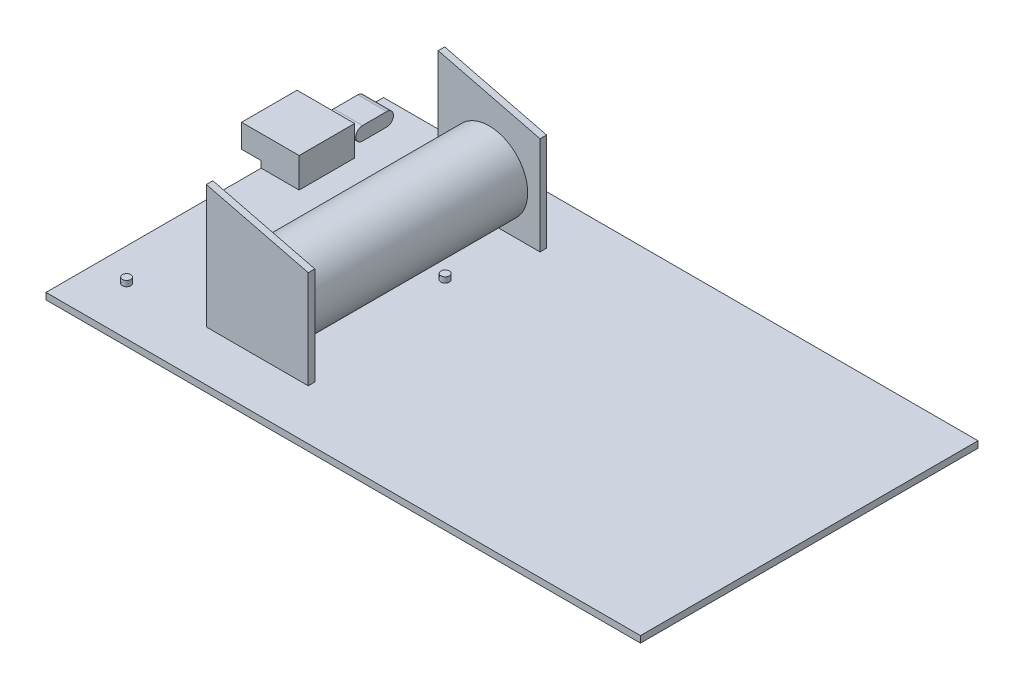
SolidWorks part; units mm, degrees
ref_plane "Front Plane" through (0, 0, 0) normal (0, 0, 1) x (1, 0, 0)
ref_plane "Top Plane" through (0, 0, 0) normal (0, 1, 0) x (1, 0, 0)
ref_plane "Right Plane" through (0, 0, 0) normal (1, 0, 0) x (0, 0, -1)
sketch "Sketch1" plane through (0, 0, 0) normal (0, 1, 0) x (1, 0, 0)
  line L1 (-70.45, -40) -> (70.45, -40)
  line L2 (-70.45, -40) -> (-70.45, 40)
  line L3 (-70.45, 40) -> (70.45, 40)
  line L4 (70.45, -40) -> (70.45, 40)
  line L5 (-70.45, -40) -> (70.45, 40) construction
  line L6 (-70.45, 40) -> (70.45, -40) construction
  point P0 (0, 0)
  dimension "D1" = 140.9
  dimension "D2" = 80
extrude "PCB" add sketch "Sketch1" along normal blind 1.55
sketch "Sketch2" plane through (-70.45, 0, 0) normal (-1, 0, 0) x (0, 0, 1)
  line L0 (-31.43, 1.55) -> (-31.43, 3.15)
  line L1 (-40, 1.55) -> (40, 1.55) construction
  line L2 (-40, 1.55) -> (-40, 0) construction
  dimension "D1" = 1.6
  dimension "D2" = 8.57
sketch "Sketch3" plane through (-70.45, 0, 0) normal (-1, 0, 0) x (0, 0, 1)
  line L0 (-34.3, 3.15) -> (-28.56, 3.15) construction
  line L1 (-34.3, 4.75) -> (-28.56, 4.75)
  line L2 (-34.3, 1.55) -> (-28.56, 1.55)
  arc A0 (-34.3, 4.75) -> (-34.3, 1.55) centre (-34.3, 3.15) ccw
  arc A1 (-28.56, 1.55) -> (-28.56, 4.75) centre (-28.56, 3.15) ccw
  point P2 (-31.43, 3.15)
  dimension "D1" = 5.74
extrude "bodyC" add sketch "Sketch3" against normal blind 6.45 and the other way blind 0.4
sketch "Sketch4" plane through (0, 1.55, 0) normal (0, 1, 0) x (1, 0, 0)
  line L0 (70.45, 40) -> (-70.45, 40) construction
  line L1 (-61.45, 11) -> (-75.1, 11)
  line L2 (-61.45, 11) -> (-61.45, 24.15)
  line L3 (-61.45, 24.15) -> (-75.1, 24.15)
  line L4 (-75.1, 11) -> (-75.1, 24.15)
  line L6 (-70.45, 28.56) -> (-70.45, -40) construction
  dimension "D1" = 13.65
  dimension "D2" = 13.15
  dimension "D3" = 15.85
  dimension "D4" = 4.65
extrude "Boss-Extrude4" add sketch "Sketch4" along normal blind 7.1 and the other way blind 1.55
sketch "Sketch5" plane through (0, 0, -11) normal (0, 0, 1) x (1, 0, 0)
  line L0 (-75.1, 0) -> (-75.1, 8.65) construction
  line L1 (-70.45, 0) -> (-75.1, 0)
  line L2 (-70.45, 0) -> (-70.45, 3.1)
  line L3 (-70.45, 3.1) -> (-75.1, 3.1)
  line L4 (-75.1, 0) -> (-75.1, 3.1)
  dimension "D1" = 3.1
extrude "Cut-Extrude3" cut sketch "Sketch5" against normal blind 14.1
sketch "Sketch11" plane through (0, 1.55, 0) normal (0, 1, 0) x (1, 0, 0)
  line L1 (-44.35, 26.85) -> (-20.2, 26.85)
  line L2 (-44.35, 26.85) -> (-44.35, 28.4)
  line L3 (-44.35, 28.4) -> (-20.2, 28.4)
  line L4 (-20.2, 26.85) -> (-20.2, 28.4)
  line L6 (70.45, 40) -> (-70.45, 40) construction
  line L7 (-70.45, 40) -> (-70.45, 34.3) construction
  dimension "D1" = 11.6
  dimension "D2" = 26.1
  dimension "D3" = 1.55
  dimension "D4" = 24.15
extrude "Boss-Extrude8" add sketch "Sketch11" along normal blind 29.25
sketch "Sketch7" plane through (0, 1.55, 0) normal (0, 1, 0) x (1, 0, 0)
  line L0 (-70.45, 11) -> (-70.45, -40) construction
  line L1 (-44.35, -28.1) -> (-20.2, -28.1)
  line L2 (-44.35, -28.1) -> (-44.35, -26.55)
  line L3 (-44.35, -26.55) -> (-20.2, -26.55)
  line L4 (-20.2, -28.1) -> (-20.2, -26.55)
  line L5 (-70.45, -40) -> (70.45, -40) construction
  dimension "D1" = 26.1
  dimension "D2" = 11.9
  dimension "D3" = 1.55
  dimension "D4" = 24.15
extrude "Boss-Extrude5" add sketch "Sketch7" along normal blind 29.25
sketch "Sketch8" plane through (0, 0, 28.1) normal (0, 0, 1) x (1, 0, 0)
  line L0 (-44.35, 30.8) -> (-20.2, 24.7787)
  line L1 (-20.2, 30.8) -> (-20.2, 1.55) construction
  line L5 (-20.2, 30.8) -> (-44.35, 30.8)
  line L6 (-20.2, 24.7787) -> (-20.2, 30.8)
  dimension "D1" = 14
extrude "Cut-Extrude4" cut sketch "Sketch8" against normal blind 89
sketch "Sketch12" plane through (0, 0, -26.85) normal (0, 0, 1) x (1, 0, 0)
  line L0 (-32.275, 1.55) -> (-32.275, 12.25)
  line L1 (-44.35, 1.55) -> (-20.2, 1.55) construction
  circle A0 centre (-32.275, 12.25) radius 9.15
  dimension "D1" = 10.7
extrude "Battery" add sketch "Sketch12" along normal blind 54
sketch "Sketch13" plane through (0, 1.55, 0) normal (0, 1, 0) x (1, 0, 0)
  line L0 (-70.45, -28.6) -> (-62.75, -28.6)
  line L1 (-70.45, 11) -> (-70.45, -40) construction
  line L2 (-70.45, -40) -> (70.45, -40) construction
  circle A0 centre (-62.75, -28.6) radius 1
  dimension "D1" = 7.7
  dimension "D2" = 11.4
extrude "Button" add sketch "Sketch13" along normal blind 1.3 contours A0
sketch "Sketch14" plane through (0, 1.55, 0) normal (0, 1, 0) x (1, 0, 0)
  line L0 (-33.45, 9.9) -> (-25.75, 9.9)
  line L3 (70.45, 40) -> (-70.45, 40) construction
  line L4 (70.45, -40) -> (70.45, 40) construction
  circle A0 centre (-25.75, 9.9) radius 1
  dimension "D3" = 96.2
  dimension "D2" = 30.1
  dimension "D1" = 7.7
extrude "Reset" add sketch "Sketch14" along normal blind 1.3 contours A0
